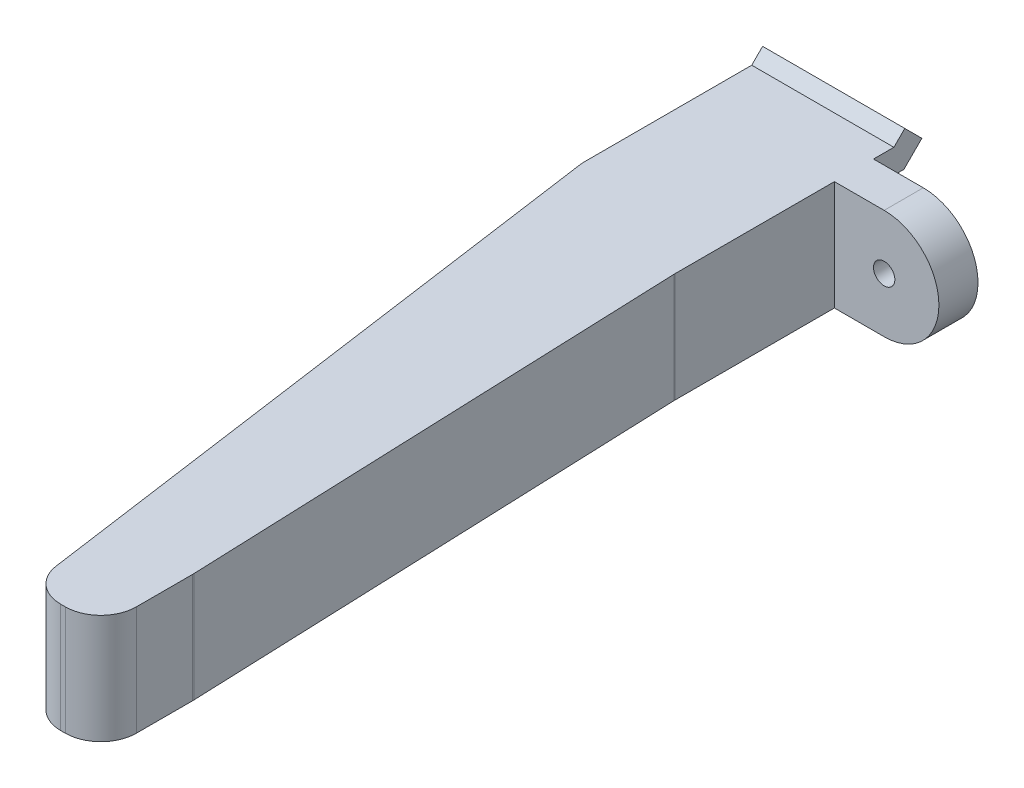
SolidWorks part; units mm, degrees
ref_plane "Front Plane" through (0, 0, 0) normal (0, 0, 1) x (1, 0, 0)
ref_plane "Top Plane" through (0, 0, 0) normal (0, 1, 0) x (1, 0, 0)
ref_plane "Right Plane" through (0, 0, 0) normal (1, 0, 0) x (0, 0, -1)
sketch "Sketch2" plane through (0, 0, 0) normal (0, 0, 1) x (1, 0, 0)
  line L0 (0, 5.9203) -> (0, 8.9503) construction
  line L1 (-5, -5.8182) -> (5, -5.8182)
  line L2 (-5, -5.8182) -> (-5, 8.9503)
  line L3 (-5, 8.9503) -> (5, 8.9503)
  line L4 (5, -5.8182) -> (5, 8.9503)
  line L5 (-20.3821, 8.9503) -> (17.3179, 8.9503) construction
  line L7 (11.6179, 5.9203) -> (-20.0072, 5.9203) construction
  line L8 (0, -5.8182) -> (0, -2.7882) construction
  point P0 (0, 0)
  dimension "D1" = 10
extrude "Boss-Extrude1" add sketch "Sketch2" along normal blind 5
sketch "Sketch8" plane through (-5, 0, 0) normal (-1, 0, 0) x (0, 0, 1)
  line L6 (-0.15, 5.7703) -> (0, 5.7703)
  line L7 (0, 8.9503) -> (0, -5.8182) construction
  line L8 (0, 5.7703) -> (0, 4.0703)
  line L9 (0, 4.0703) -> (-0.15, 4.0703)
  line L11 (-0.15, -1.9297) -> (0, -1.9297)
  line L12 (-2.1379, 4.0703) -> (-0.15, 4.0703)
  line L13 (-0.15, 4.0703) -> (-0.15, 5.7703)
  line L14 (-0.15, 5.7703) -> (-1.4337, 5.7703)
  line L15 (-1.4337, 5.7703) -> (-2.2, 6.5366)
  line L16 (-2.2, 6.5366) -> (-3.4021, 5.3345)
  line L17 (-3.4021, 5.3345) -> (-2.1379, 4.0703)
  line L18 (-2.1379, 4.0703) -> (-0.15, 4.0703)
  line L20 (-0.15, 5.7703) -> (-1.4337, 5.7703)
  line L21 (-1.4337, 5.7703) -> (-2.2, 6.5366)
  line L22 (-2.2, 6.5366) -> (-3.4021, 5.3345)
  line L23 (-3.4021, 5.3345) -> (-2.1379, 4.0703)
  line L24 (-2.1379, -1.9297) -> (-0.15, -1.9297)
  line L25 (-0.15, -1.9297) -> (-0.15, -0.2297)
  line L26 (-0.15, -0.2297) -> (-1.4337, -0.2297)
  line L27 (-1.4337, -0.2297) -> (-2.2, 0.5366)
  line L28 (-2.2, 0.5366) -> (-3.4021, -0.6655)
  line L29 (-3.4021, -0.6655) -> (-2.1379, -1.9297)
  line L30 (-2.1379, -1.9297) -> (-0.15, -1.9297)
  line L32 (-0.15, -0.2297) -> (-1.4337, -0.2297)
  line L33 (-1.4337, -0.2297) -> (-2.2, 0.5366)
  line L34 (-2.2, 0.5366) -> (-3.4021, -0.6655)
  line L35 (-3.4021, -0.6655) -> (-2.1379, -1.9297)
  line L37 (-0.15, -0.2297) -> (0, -0.2297)
  line L38 (0, -1.9297) -> (0, -0.2297)
  dimension "D1" = 0.15
  dimension "D2" = 0.15
extrude "Boss-Extrude4" add sketch "Sketch8" against normal up to surface (10 mm away) up to face at (5, 1.566, 2.5)
sketch "Sketch9" plane through (0, 0, 0) normal (0, 0, -1) x (-1, 0, 0)
  line L4 (-5, 8.9503) -> (-5, 5.7703)
  line L5 (-5, 5.7703) -> (5, 5.7703)
  line L6 (5, 5.7703) -> (5, 8.9503)
  line L7 (5, 8.9503) -> (-5, 8.9503)
  line L8 (-5, 8.9503) -> (-5, 5.7703)
  line L10 (5, 5.7703) -> (5, 8.9503)
  line L11 (5, 8.9503) -> (-5, 8.9503)
  line L16 (5, -1.9297) -> (-5, -1.9297)
  line L17 (-5, -1.9297) -> (-5, -5.8182)
  line L18 (-5, -5.8182) -> (5, -5.8182)
  line L19 (5, -5.8182) -> (5, -1.9297)
  line L21 (-5, -1.9297) -> (-5, -5.8182)
  line L22 (-5, -5.8182) -> (5, -5.8182)
  line L23 (5, -5.8182) -> (5, -1.9297)
  line L26 (-5, 5.7703) -> (5, 5.7703)
  line L27 (5, -1.9297) -> (-5, -1.9297)
  dimension "D1" = 0
  dimension "D2" = 0
extrude "Cut-Extrude3" cut sketch "Sketch9" against normal blind 5
sketch "Sketch10" plane through (0, 5.7703, 0) normal (0, 1, 0) x (1, 0, 0)
  line L0 (-5, -5) -> (-5, -10.5)
  line L1 (-5, -10.5) -> (1.3524, -55.7)
  line L2 (1.3524, -55.7) -> (6.3524, -55.7)
  line L3 (-5, -5) -> (5, -5)
  line L4 (-120.9789, 453.7107) -> (412.3545, 453.7107) construction
  line L5 (6.3524, -55.7) -> (6.3524, -49.2)
  line L6 (5, -5) -> (5, -14)
  line L7 (5, -14) -> (6.3524, -49.2)
  dimension "D1" = 172
  dimension "D2" = 45.2
  dimension "D3" = 5
  dimension "D4" = 6.5
  dimension "D5" = 5.5
  dimension "D6" = 9
extrude "Boss-Extrude5" add sketch "Sketch10" against normal up to surface (7.7 mm away) up to face at (0, -1.9297, 1.4311)
ref_plane "Plane1" through (0, 0, 2.75) normal (0, 0, 1) x (1, 0, 0)
sketch "Sketch12" plane through (0, 0, 0) normal (0, 0, 1) x (1, 0, 0)
  line L0 (5, 5.7703) -> (8.5, 5.7703)
  line L1 (8.5, -1.9297) -> (5, -1.9297)
  line L2 (5, -1.9297) -> (5, 5.7703)
  line L3 (1.3524, 5.7703) -> (6.3524, 5.7703) construction
  line L4 (1.3524, -1.9297) -> (6.3524, -1.9297) construction
  line L5 (5, 5.3345) -> (5, 6.5366) construction
  line L6 (6.3524, 5.7703) -> (5, 5.7703) construction
  arc A0 (8.5, 5.7703) -> (8.5, -1.9297) centre (8.5, 1.9203) cw
  circle A1 centre (8.5, 1.9203) radius 0.75
  dimension "D1" = 1.5
  dimension "D2" = 3.5
extrude "Boss-Extrude7" add sketch "Sketch12" along normal up to surface (2.75 mm away) up to plane "Plane1"
fillet "Fillet1" radius 2.5 4 edges at (6.3524, 1.9203, 49.2) (5, 1.9203, 14) (1.3524, 1.9203, 55.7) (6.3524, 1.9203, 55.7)
sketch "Sketch13" plane through (6.3524, 0, 0) normal (1, 0, 0) x (0, 0, -1)
  line L0 (-49.248, -1.9297) -> (-49.248, 5.7703) construction
  point P0 (-49.248, 1.9203)
